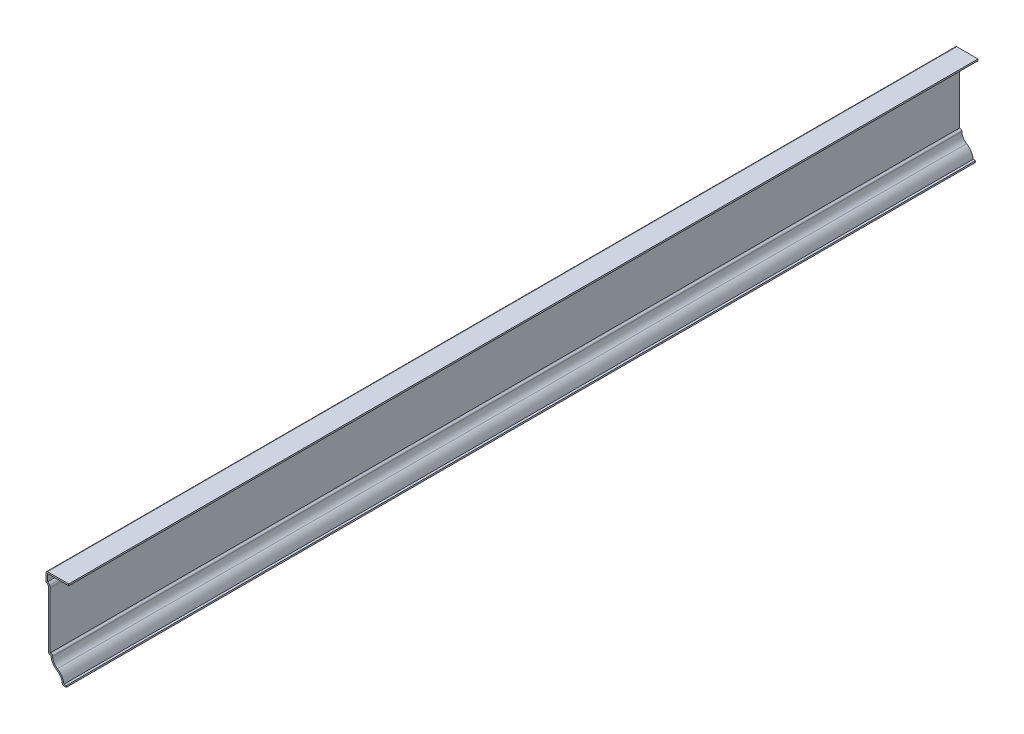
SolidWorks part; units mm, degrees
ref_plane "Front Plane" through (0, 0, 0) normal (0, 0, 1) x (1, 0, 0)
ref_plane "Top Plane" through (0, 0, 0) normal (0, 1, 0) x (1, 0, 0)
ref_plane "Right Plane" through (0, 0, 0) normal (1, 0, 0) x (0, 0, -1)
sketch "Sketch1" plane through (0, 0, 0) normal (0, 0, 1) x (1, 0, 0)
  line L0 (0, 0) -> (-2.3813, 0)
  line L1 (-9.525, 12.7) -> (-11.1125, 12.7)
  line L2 (-11.1125, 12.7) -> (-11.1125, 49.2125)
  line L3 (-12.7, 50.8) -> (-12.7, 57.15)
  line L4 (-12.7, 57.15) -> (1.5875, 57.15)
  line L5 (-11.1125, 12.7) -> (-2.3813, 12.7) construction
  arc A0 (-2.3813, 0) -> (-6.0909, 6.595) centre (-10.0983, 0) ccw
  arc A1 (-6.0909, 6.595) -> (-9.525, 12.7) centre (-2.3813, 12.7) cw
  arc A2 (-11.1125, 49.2125) -> (-12.7, 50.8) centre (-12.7, 49.2125) ccw
  dimension "D1" = 14.2875
  dimension "D2" = 2.3813
  dimension "D3" = 7.1437
  dimension "D4" = 12.7
  dimension "D5" = 1.5875
  dimension "D6" = 38.1
  dimension "D7" = 6.35
  dimension "D8" = 1.5875
extrude "Extrude-Thin1" add sketch "Sketch1" against normal blind 571.5 thin
fillet "Fillet1" radius 1.016 5 edges at (-2.3813, 0, -285.75) (-8.4242, 13.716, -285.75) (-11.1125, 12.7, -285.75) (-12.7, 50.8, -285.75) (-12.7, 57.15, -285.75)
